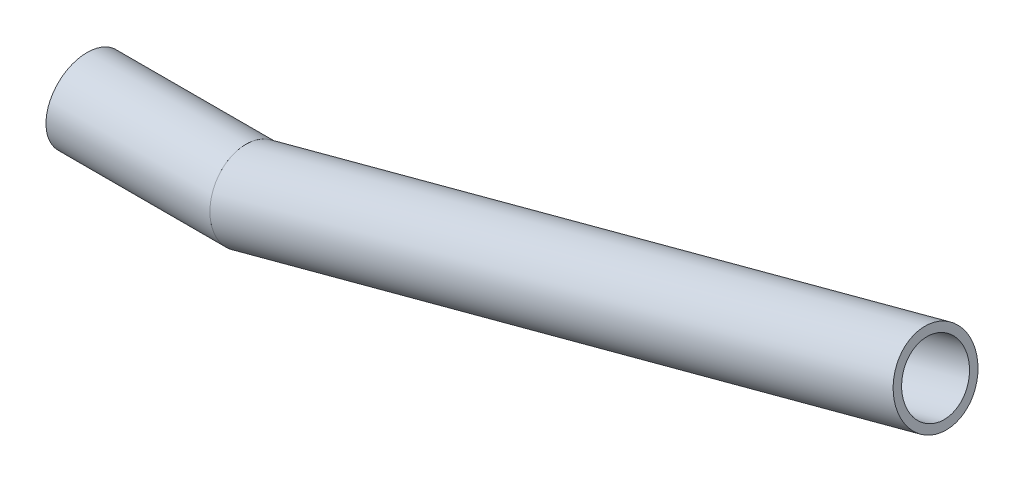
SolidWorks part; units mm, degrees
ref_plane "Front Plane" through (0, 0, 0) normal (0, 0, 1) x (1, 0, 0)
ref_plane "Top Plane" through (0, 0, 0) normal (0, 1, 0) x (1, 0, 0)
ref_plane "Right Plane" through (0, 0, 0) normal (1, 0, 0) x (0, 0, -1)
sketch "Sketch2" plane through (0, 0, 0) normal (0, 0, 1) x (1, 0, 0)
  line L0 (-77.8723, 14.641) -> (125.953, 14.641) construction
  line L1 (-107.3181, 25.8935) -> (-56.5181, 25.8935)
  line L2 (-56.5181, 25.8935) -> (154.9694, 82.5614)
  line L3 (154.9694, 82.5614) -> (154.9694, -84.4353) construction
  line L4 (-56.5181, 25.8935) -> (-56.5181, -136.7296) construction
  line L5 (189.8569, 74.1051) -> (189.8569, -336.1283) construction
  dimension "D1" = 165
  dimension "D2" = 50.8
  dimension "D3" = 218.948
ref_plane "Plane1" through (-107.3181, 25.8935, 0) normal (1, 0, 0) x (0, 1, 0)
ref_plane "Plane2" through (-56.5181, 25.8935, 0) normal (0.9659, 0.2588, 0) x (-0.2588, 0.9659, 0)
other "Tubing TUBING(1)"
ref_plane "Plane3" through (-107.3181, 25.8935, 0) normal (1, 0, 0) x (0, 1, 0)
sketch "Sketch1" plane through (-107.3181, 25.8935, 0) normal (1, 0, 0) x (0, 1, 0)
  circle A0 centre (0, 0) radius 12.7
  circle A1 centre (0, 0) radius 10.16
  point P5 (0, 12.7)
  point P6 (0, 10.16)
  point P7 (0, -12.7)
  point P8 (0, -10.16)
  point P9 (0, 0)
  dimension "D1" = 25.4
  dimension "D2" = 2.54
ref_plane "Plane4" through (0, 0, 0) normal (0, 0, 1) x (0.9659, 0.2588, 0)
sketch "Sketch4" plane through (0, 0, 0) normal (0, 0, 1) x (0.9659, 0.2588, 0)
  line L0 (-94.2424, 92.016) -> (189.7443, 90.3435) construction
sketch "Sketch5" plane through (-107.3181, 25.8935, 0) normal (1, 0, 0) x (0, 1, 0)
  line L0 (12.7, 0) -> (-12.7, 0) construction
  circle A0 centre (0, 0) radius 12.7 construction
  circle A1 centre (0, 0) radius 10.16 construction
  point P5 (-10.16, 0)
sketch "Sketch6" plane through (165.2288, 44.2729, 0) normal (0.9659, 0.2588, 0) x (0, 0, -1)
  line L0 (0, 52.3392) -> (0, 26.9392) construction
  circle A0 centre (0, 39.6392) radius 12.7 construction
